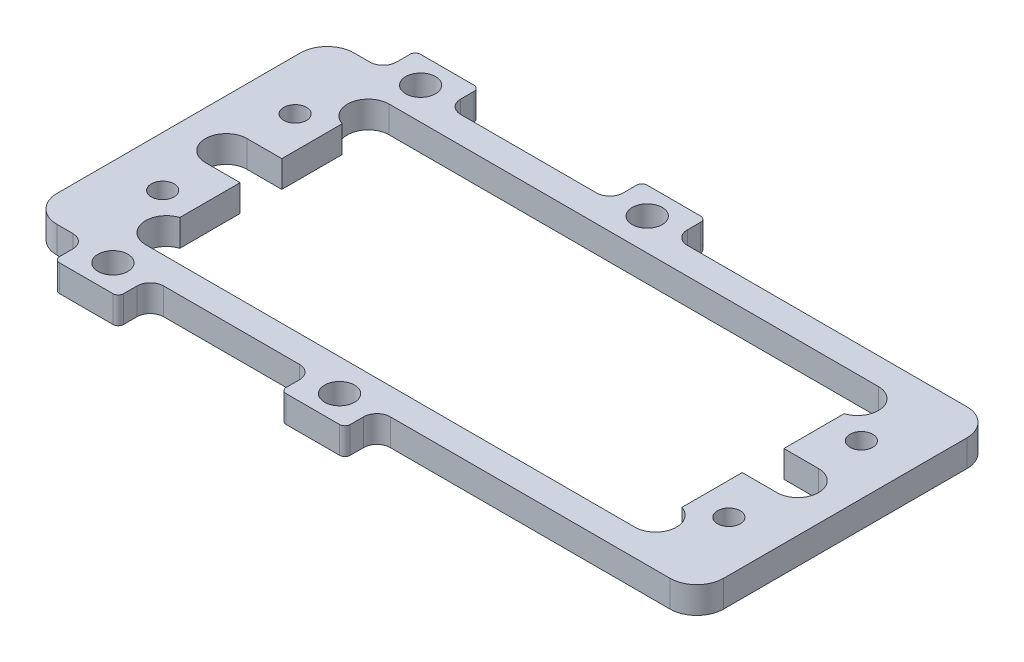
SolidWorks part; units mm, degrees
ref_plane "Front Plane" through (0, 0, 0) normal (0, 0, 1) x (1, 0, 0)
ref_plane "Top Plane" through (0, 0, 0) normal (0, 1, 0) x (1, 0, 0)
ref_plane "Right Plane" through (0, 0, 0) normal (1, 0, 0) x (0, 0, -1)
ref_plane "Plane1" through (0, 0, 0) normal (0, -1, 0) x (1, 0, 0)
sketch "Sketch1" plane through (0, 0, 0) normal (0, -1, 0) x (1, 0, 0)
  line L0 (-6.0223, -19.2405) -> (-6.0223, -20.828)
  line L1 (-5.3873, -21.463) -> (0.9627, -21.463)
  line L2 (1.5977, -20.828) -> (1.5977, -19.2405)
  line L3 (3.1852, -17.653) -> (36.4312, -17.653)
  line L4 (39.624, -14.4602) -> (39.624, 14.4602)
  line L5 (36.4312, 17.653) -> (3.1852, 17.653)
  line L6 (1.5977, 19.2405) -> (1.5977, 20.828)
  line L7 (0.9627, 21.463) -> (-5.3873, 21.463)
  line L8 (-6.0223, 20.828) -> (-6.0223, 19.2405)
  line L9 (-7.6098, 17.653) -> (-23.7556, 17.653)
  line L10 (-25.3431, 19.2405) -> (-25.3431, 20.828)
  line L11 (-25.9781, 21.463) -> (-32.3281, 21.463)
  line L12 (-32.9631, 20.828) -> (-32.9631, 19.2405)
  line L13 (-34.5506, 17.653) -> (-36.4312, 17.653)
  line L14 (-39.624, 14.4602) -> (-39.624, -14.4602)
  line L15 (-36.4312, -17.653) -> (-34.5506, -17.653)
  line L16 (-32.9631, -19.2405) -> (-32.9631, -20.828)
  line L17 (-32.3281, -21.463) -> (-25.9781, -21.463)
  line L18 (-25.3431, -20.828) -> (-25.3431, -19.2405)
  line L19 (-23.7556, -17.653) -> (-7.6098, -17.653)
  line L20 (-33.9725, 2.4765) -> (-29.845, 2.4765)
  line L21 (-29.845, 2.4765) -> (-29.845, 9.646)
  line L22 (-29.0805, 14.478) -> (29.0805, 14.478)
  line L23 (29.845, 9.646) -> (29.845, 2.4765)
  line L24 (29.845, 2.4765) -> (33.9725, 2.4765)
  line L25 (33.9725, -2.4765) -> (29.845, -2.4765)
  line L26 (29.845, -2.4765) -> (29.845, -9.646)
  line L27 (29.0805, -14.478) -> (-29.0805, -14.478)
  line L28 (-29.845, -9.646) -> (-29.845, -2.4765)
  line L29 (-29.845, -2.4765) -> (-33.9725, -2.4765)
  line L30 (-31.8783, -10.1653) -> (-30.9939, -15.7548) construction
  line L31 (-36.449, 17.653) -> (-36.449, -17.653) construction
  line L32 (36.4668, 17.653) -> (36.4312, -17.653) construction
  circle A0 centre (33.655, -7.874) radius 1.3525
  circle A1 centre (-33.655, 7.874) radius 1.3525
  circle A2 centre (-33.655, -7.874) radius 1.3525
  circle A3 centre (-2.2123, 18.288) radius 1.778
  circle A4 centre (-29.1531, -18.288) radius 1.778
  circle A5 centre (-2.2123, -18.288) radius 1.778
  arc A6 (-6.0223, -20.828) -> (-5.3873, -21.463) centre (-5.3873, -20.828) ccw
  arc A7 (0.9627, -21.463) -> (1.5977, -20.828) centre (0.9627, -20.828) ccw
  arc A8 (1.5977, -19.2405) -> (3.1852, -17.653) centre (3.1852, -19.2405) cw
  arc A9 (36.4312, -17.653) -> (39.624, -14.4602) centre (36.4312, -14.4602) ccw
  arc A10 (39.624, 14.4602) -> (36.4312, 17.653) centre (36.4312, 14.4602) ccw
  arc A11 (3.1852, 17.653) -> (1.5977, 19.2405) centre (3.1852, 19.2405) cw
  arc A12 (1.5977, 20.828) -> (0.9627, 21.463) centre (0.9627, 20.828) ccw
  arc A13 (-5.3873, 21.463) -> (-6.0223, 20.828) centre (-5.3873, 20.828) ccw
  arc A14 (-6.0223, 19.2405) -> (-7.6098, 17.653) centre (-7.6098, 19.2405) cw
  arc A15 (-23.7556, 17.653) -> (-25.3431, 19.2405) centre (-23.7556, 19.2405) cw
  arc A16 (-25.3431, 20.828) -> (-25.9781, 21.463) centre (-25.9781, 20.828) ccw
  arc A17 (-32.3281, 21.463) -> (-32.9631, 20.828) centre (-32.3281, 20.828) ccw
  arc A18 (-32.9631, 19.2405) -> (-34.5506, 17.653) centre (-34.5506, 19.2405) cw
  arc A19 (-36.4312, 17.653) -> (-39.624, 14.4602) centre (-36.4312, 14.4602) ccw
  arc A20 (-39.624, -14.4602) -> (-36.4312, -17.653) centre (-36.4312, -14.4602) ccw
  arc A21 (-34.5506, -17.653) -> (-32.9631, -19.2405) centre (-34.5506, -19.2405) cw
  arc A22 (-32.9631, -20.828) -> (-32.3281, -21.463) centre (-32.3281, -20.828) ccw
  arc A23 (-25.9781, -21.463) -> (-25.3431, -20.828) centre (-25.9781, -20.828) ccw
  arc A24 (-25.3431, -19.2405) -> (-23.7556, -17.653) centre (-23.7556, -19.2405) cw
  arc A25 (-7.6098, -17.653) -> (-6.0223, -19.2405) centre (-7.6098, -19.2405) cw
  circle A26 centre (-29.1531, 18.288) radius 1.778
  circle A27 centre (33.655, 7.874) radius 1.3525
  arc A28 (-29.845, 9.646) -> (-29.0805, 14.478) centre (-29.0805, 12.0015) cw
  arc A29 (29.0805, 14.478) -> (29.845, 9.646) centre (29.0805, 12.0015) cw
  arc A30 (33.9725, 2.4765) -> (33.9725, -2.4765) centre (33.9725, 0) cw
  arc A31 (29.845, -9.646) -> (29.0805, -14.478) centre (29.0805, -12.0015) cw
  arc A32 (-29.0805, -14.478) -> (-29.845, -9.646) centre (-29.0805, -12.0015) cw
  arc A33 (-33.9725, -2.4765) -> (-33.9725, 2.4765) centre (-33.9725, 0) cw
  point P98 (-31.5265, -12.3885)
  point P104 (-36.449, 0)
  point P107 (36.449, 0)
  dimension "D2" = 36.576
  dimension "D4" = 72.8624
  dimension "D1" = 6.985
  dimension "D3" = 9.779
extrude "Boss-Extrude1" add sketch "Sketch1" against normal blind 3.175
